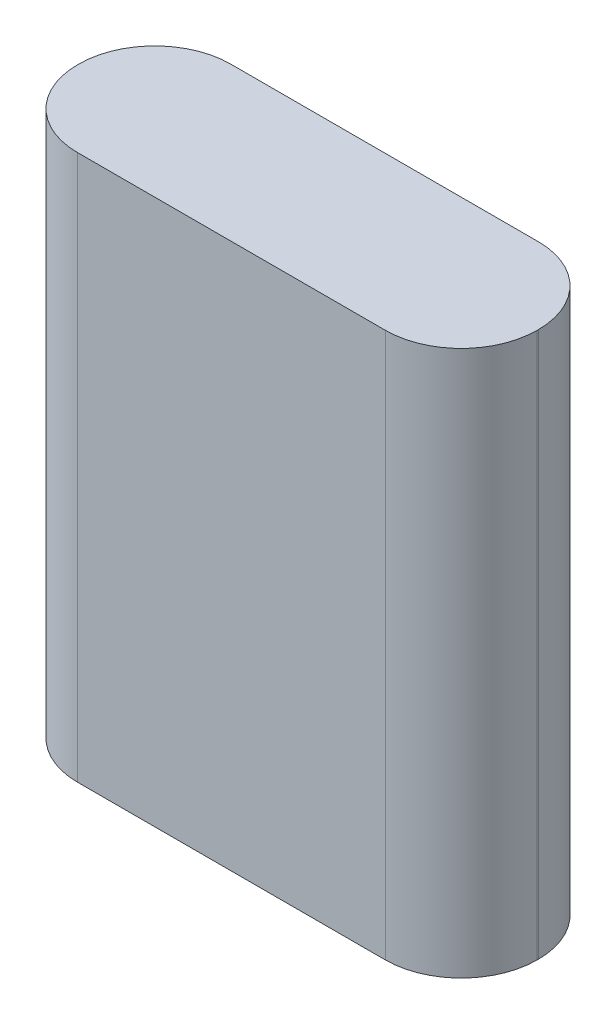
SolidWorks part; units mm, degrees
material "Custom Plastic"
ref_plane "Front Plane" through (0, 0, 0) normal (0, 0, 1) x (1, 0, 0)
ref_plane "Top Plane" through (0, 0, 0) normal (0, 1, 0) x (1, 0, 0)
ref_plane "Right Plane" through (0, 0, 0) normal (1, 0, 0) x (0, 0, -1)
sketch "Sketch1" plane through (0, 0, 0) normal (0, 1, 0) x (1, 0, 0)
  line L1 (-21.5, 7.165) -> (21.5, 7.165)
  line L2 (-21.5, 7.165) -> (-21.5, -7.165)
  line L3 (-21.5, -7.165) -> (21.5, -7.165)
  line L4 (21.5, 7.165) -> (21.5, -7.165)
  line L5 (-21.5, 7.165) -> (21.5, -7.165) construction
  line L6 (-21.5, -7.165) -> (21.5, 7.165) construction
  point P0 (0, 0)
  dimension "D1" = 14.33
  dimension "D2" = 43
extrude "Boss-Extrude1" add sketch "Sketch1" along normal blind 51
fillet "Fillet1" radius 7.1 4 edges at (21.5, 25.5, -7.165) (21.5, 25.5, 7.165) (-21.5, 25.5, -7.165) (-21.5, 25.5, 7.165)
